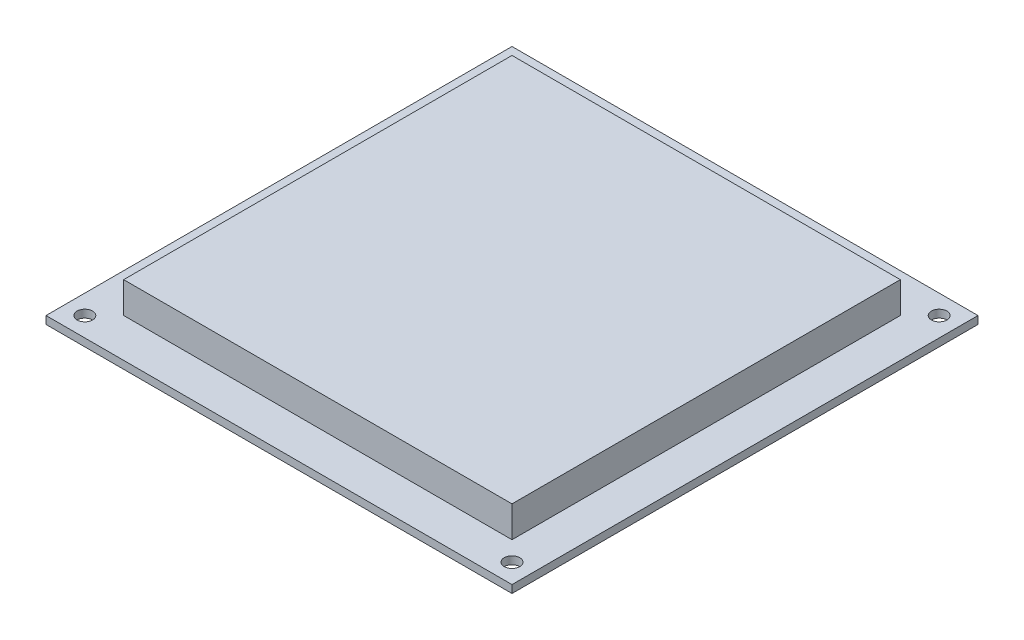
SolidWorks part; units mm, degrees
ref_plane "Front Plane" through (0, 0, 0) normal (0, 0, 1) x (1, 0, 0)
ref_plane "Top Plane" through (0, 0, 0) normal (0, 1, 0) x (1, 0, 0)
ref_plane "Right Plane" through (0, 0, 0) normal (1, 0, 0) x (0, 0, -1)
sketch "Sketch1" plane through (0, 0, 0) normal (0, 1, 0) x (1, 0, 0)
  line L1 (-76.2, 76.2) -> (76.2, 76.2)
  line L2 (-76.2, 76.2) -> (-76.2, -76.2)
  line L3 (-76.2, -76.2) -> (76.2, -76.2)
  line L4 (76.2, 76.2) -> (76.2, -76.2)
  line L5 (-76.2, 76.2) -> (76.2, -76.2) construction
  line L6 (-76.2, -76.2) -> (76.2, 76.2) construction
  point P0 (0, 0)
  dimension "D1" = 152.4
  dimension "D2" = 152.4
extrude "Boss-Extrude1" add sketch "Sketch1" against normal blind 2.54
sketch "Sketch9" plane through (0, 0, 0) normal (0, 1, 0) x (1, 0, 0)
  line L0 (-76.2, -76.2) -> (76.2, -76.2) construction
  line L1 (-76.2, 76.2) -> (-76.2, -76.2) construction
  line L2 (76.2, -76.2) -> (76.2, 76.2) construction
  line L3 (76.2, 76.2) -> (-76.2, 76.2) construction
  circle A0 centre (-69.85, -69.85) radius 2.54
  circle A1 centre (69.85, -69.85) radius 2.54
  circle A2 centre (69.85, 69.85) radius 2.54
  circle A3 centre (-69.85, 69.85) radius 2.54
  dimension "D3" = 5.08
  dimension "D4" = 5.08
  dimension "D6" = 5.08
  dimension "D7" = 5.08
  dimension "D1" = 6.35
  dimension "D2" = 6.35
  dimension "D5" = 6.35
  dimension "D8" = 6.35
  dimension "D9" = 6.35
  dimension "D10" = 6.35
  dimension "D11" = 6.35
  dimension "D12" = 6.35
extrude "Cut-Extrude5" cut sketch "Sketch9" against normal through all
sketch "Sketch10" plane through (0, 0, 0) normal (0, 1, 0) x (1, 0, 0)
  line L1 (-63.5, 63.5) -> (63.5, 63.5)
  line L2 (-63.5, 63.5) -> (-63.5, -63.5)
  line L3 (-63.5, -63.5) -> (63.5, -63.5)
  line L4 (63.5, 63.5) -> (63.5, -63.5)
  line L5 (-63.5, 63.5) -> (63.5, -63.5) construction
  line L6 (-63.5, -63.5) -> (63.5, 63.5) construction
  point P0 (0, 0)
  dimension "D1" = 127
  dimension "D2" = 127
extrude "Boss-Extrude2" add sketch "Sketch10" along normal blind 10.16
